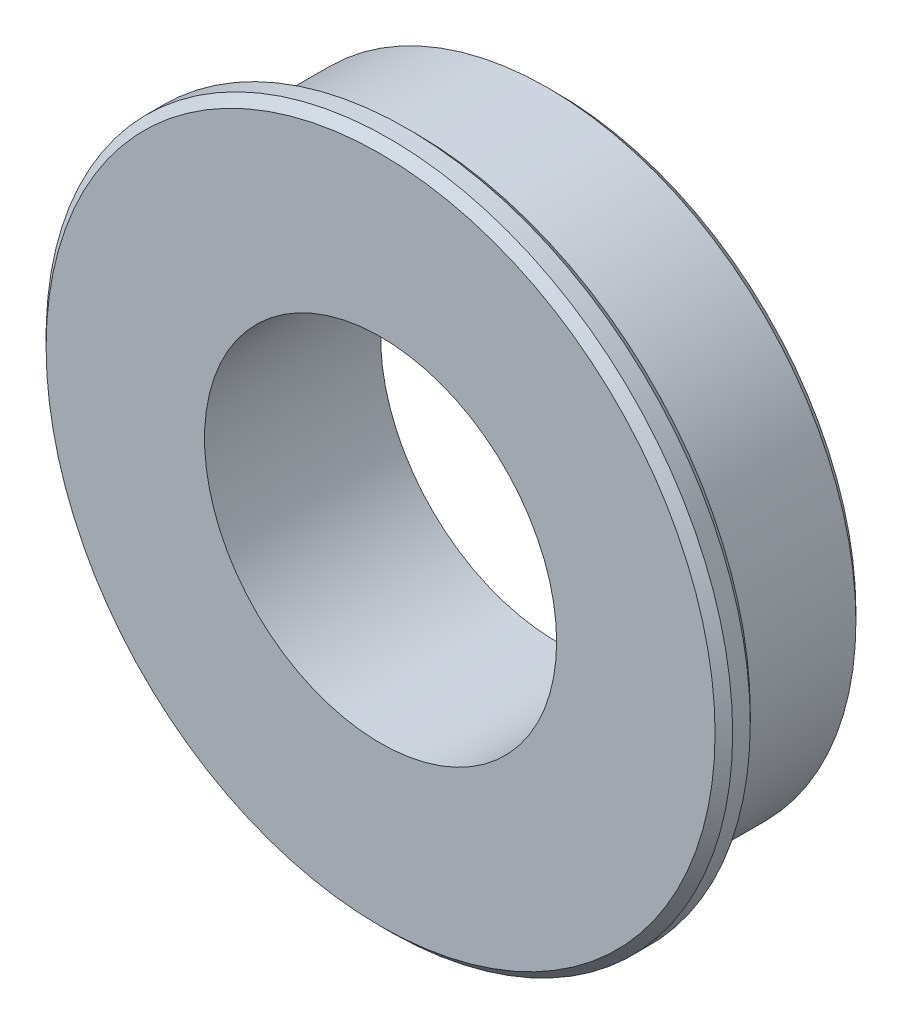
SolidWorks part; units mm, degrees
ref_plane "前视基准面" through (0, 0, 0) normal (0, 0, 1) x (1, 0, 0)
ref_plane "上视基准面" through (0, 0, 0) normal (0, 1, 0) x (1, 0, 0)
ref_plane "右视基准面" through (0, 0, 0) normal (1, 0, 0) x (0, 0, -1)
sketch "草图1" plane through (0, 0, 0) normal (0, 0, 1) x (1, 0, 0)
  circle A0 centre (0, 0) radius 7
  circle A1 centre (0, 0) radius 4
  dimension "D1" = 14
  dimension "D2" = 8
extrude "凸台-拉伸1" add sketch "草图1" along normal mid plane 4
sketch "草图2" plane through (0, 0, 2) normal (0, 0, 1) x (1, 0, 0)
  circle A0 centre (0, 0) radius 7.8
  circle A2 centre (0, 0) radius 4 construction
  circle A3 centre (0, 0) radius 4
  dimension "D1" = 15.6
extrude "凸台-拉伸2" add sketch "草图2" against normal blind 0.8
chamfer "倒角1" distance 0.2 angle 45 3 edges at (7, 0, -2) (7.8, 0, 1.2) (7.8, 0, 2)
